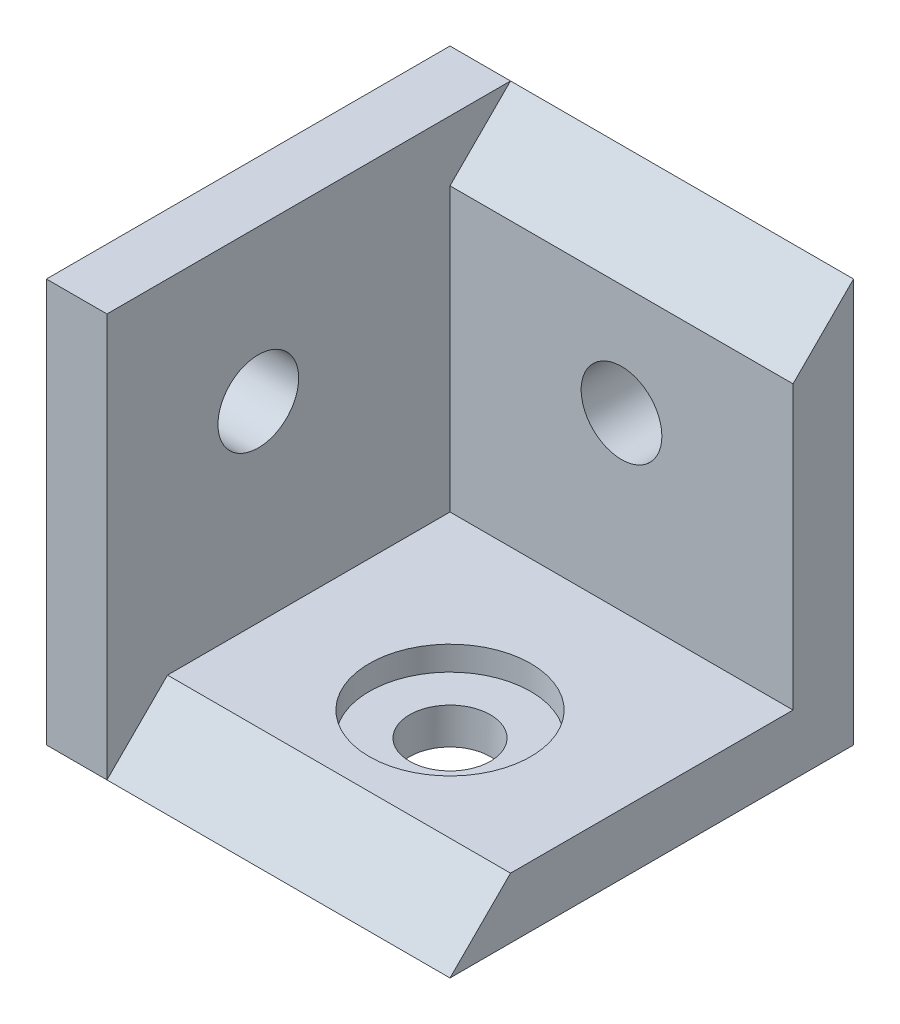
SolidWorks part; units mm, degrees
ref_plane "Front Plane" through (0, 0, 0) normal (0, 0, 1) x (1, 0, 0)
ref_plane "Top Plane" through (0, 0, 0) normal (0, 1, 0) x (1, 0, 0)
ref_plane "Right Plane" through (0, 0, 0) normal (1, 0, 0) x (0, 0, -1)
sketch "Çizim1" plane through (0, 0, 0) normal (0, 1, 0) x (1, 0, 0)
  line L1 (0, 0) -> (20, 0)
  line L2 (0, 0) -> (0, 20)
  line L3 (0, 20) -> (20, 20)
  line L4 (20, 0) -> (20, 20)
extrude "Yükseklik-Ekstrüzyon1" add sketch "Çizim1" along normal blind 20
sketch "Çizim2" plane through (20, 0, 0) normal (1, 0, 0) x (0, 0, -1)
  line L0 (20, 20) -> (0, 0)
  line L1 (0, 0) -> (0, 20)
  line L2 (0, 20) -> (20, 20)
extrude "Kes-Ekstrüzyon1" cut sketch "Çizim2" against normal blind 17
sketch "Çizim3" plane through (20, 0, 0) normal (1, 0, 0) x (0, 0, -1)
  line L5 (17, 3) -> (-0.3263, 3)
  line L6 (17, 3) -> (17, 20.9197)
  line L7 (17, 20.9197) -> (-0.3263, 20.9197)
  line L8 (-0.3263, 3) -> (-0.3263, 20.9197)
extrude "Kes-Ekstrüzyon2" cut sketch "Çizim3" against normal blind 17
sketch "Çizim4" plane through (0, 0, -17) normal (0, 0, 1) x (1, 0, 0)
  line L0 (3, 20) -> (20, 3) construction
  circle A0 centre (11.5, 11.5) radius 2
sketch "Çizim5" plane through (0, 3, 0) normal (0, 1, 0) x (1, 0, 0)
  line L0 (20, 0) -> (3, 17) construction
  circle A0 centre (11.5, 8.5) radius 2
sketch "Çizim6" plane through (3, 0, 0) normal (1, 0, 0) x (0, 0, -1)
  circle A0 centre (7.5, 12.5) radius 2
extrude "Kes-Ekstrüzyon3" cut sketch "Çizim6" against normal blind 17 contours A0
sketch "Çizim7" plane through (0, 0, -17) normal (0, 0, 1) x (1, 0, 0)
  line L0 (3, 20) -> (20, 3) construction
  circle A1 centre (11.5, 11.5) radius 2
extrude "Kes-Ekstrüzyon4" cut sketch "Çizim7" against normal blind 17
extrude "Kes-Ekstrüzyon5" cut sketch "Çizim5" against normal blind 17 contours A0
sketch "Çizim8" plane through (0, 3, 0) normal (0, 1, 0) x (1, 0, 0)
  circle A0 centre (11.5, 8.5) radius 4
extrude "Kes-Ekstrüzyon6" cut sketch "Çizim8" against normal blind 1.2
